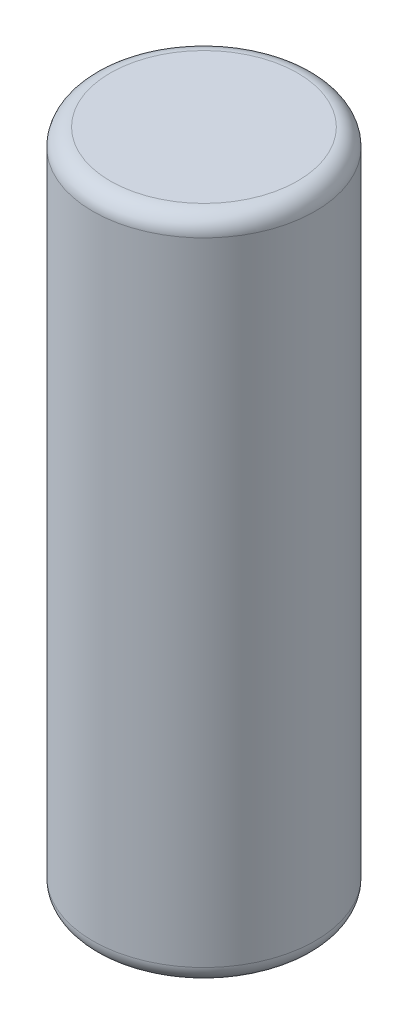
SolidWorks part; units mm, degrees
ref_plane "Front Plane" through (0, 0, 0) normal (0, 0, 1) x (1, 0, 0)
ref_plane "Top Plane" through (0, 0, 0) normal (0, 1, 0) x (1, 0, 0)
ref_plane "Right Plane" through (0, 0, 0) normal (1, 0, 0) x (0, 0, -1)
sketch "Sketch1" plane through (0, 0, 0) normal (0, 1, 0) x (1, 0, 0)
  circle A0 centre (0, 0) radius 3.175
  dimension "D1" = 6.35
extrude "Boss-Extrude1" add sketch "Sketch1" along normal blind 19.05
fillet "Fillet1" radius 0.5 2 edges at (0, 0, 3.175) (0, 19.05, 3.175)
